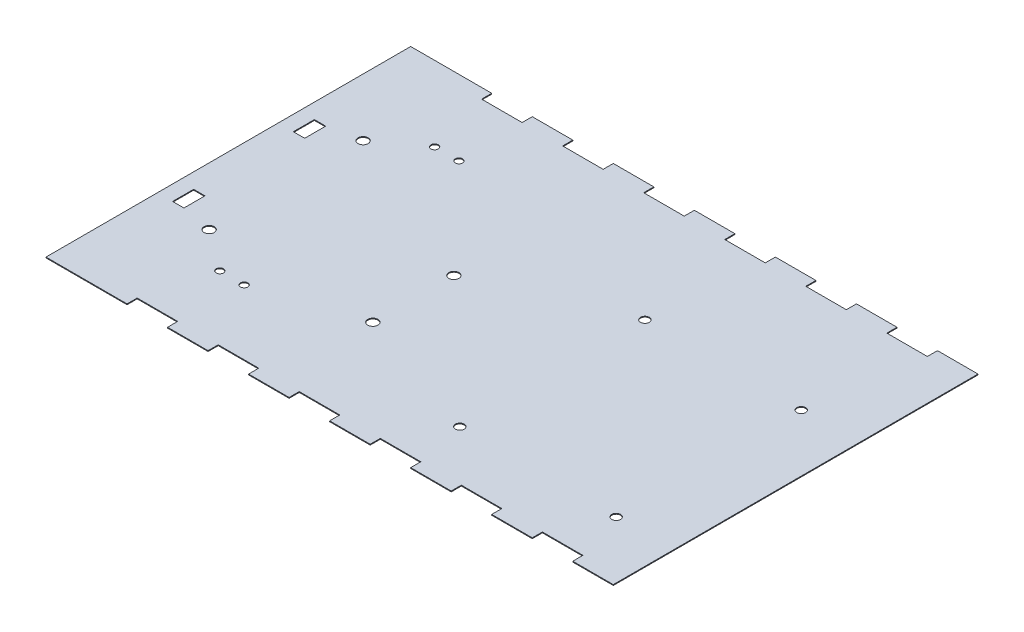
SolidWorks part; units mm, degrees
ref_plane "Front" through (0, 0, 0) normal (0, 0, 1) x (1, 0, 0)
ref_plane "Top" through (0, 0, 0) normal (0, 1, 0) x (1, 0, 0)
ref_plane "Right" through (0, 0, 0) normal (1, 0, 0) x (0, 0, -1)
sketch "Sketch1" plane through (0, 0, 0) normal (0, 1, 0) x (1, 0, 0)
  line L1 (-88.9, -57.15) -> (88.9, -57.15)
  line L2 (-88.9, -57.15) -> (-88.9, 57.15)
  line L3 (-88.9, 57.15) -> (88.9, 57.15)
  line L4 (88.9, -57.15) -> (88.9, 57.15)
  line L5 (-88.9, -57.15) -> (88.9, 57.15) construction
  line L6 (-88.9, 57.15) -> (88.9, -57.15) construction
  point P0 (0, 0)
  dimension "D1" = 177.8
  dimension "D2" = 114.3
extrude "Boss-Extrude1" add sketch "Sketch1" along normal blind 0.254
sketch "Sketch2" plane through (0, 0.254, 0) normal (0, 1, 0) x (1, 0, 0)
  line L0 (-73.152, -57.15) -> (-73.152, 57.15) construction
  line L1 (-88.9, -57.15) -> (88.9, -57.15) construction
  line L2 (88.9, 57.15) -> (-88.9, 57.15) construction
  line L3 (88.9, -57.15) -> (88.9, 57.15) construction
  line L4 (76.2, -57.15) -> (63.5, -57.15)
  line L5 (76.2, -57.15) -> (76.2, -53.975)
  line L6 (76.2, -53.975) -> (63.5, -53.975)
  line L7 (63.5, -57.15) -> (63.5, -53.975)
  line L8 (50.8, -57.15) -> (50.8, -53.975)
  line L9 (50.8, -57.15) -> (38.1, -57.15)
  line L10 (38.1, -57.15) -> (38.1, -53.975)
  line L11 (50.8, -53.975) -> (38.1, -53.975)
  line L12 (25.4, -57.15) -> (25.4, -53.975)
  line L13 (25.4, -57.15) -> (12.7, -57.15)
  line L14 (12.7, -57.15) -> (12.7, -53.975)
  line L15 (25.4, -53.975) -> (12.7, -53.975)
  line L16 (0, -57.15) -> (0, -53.975)
  line L17 (0, -57.15) -> (-12.7, -57.15)
  line L18 (-12.7, -57.15) -> (-12.7, -53.975)
  line L19 (0, -53.975) -> (-12.7, -53.975)
  line L20 (-25.4, -57.15) -> (-25.4, -53.975)
  line L21 (-25.4, -57.15) -> (-38.1, -57.15)
  line L22 (-38.1, -57.15) -> (-38.1, -53.975)
  line L23 (-25.4, -53.975) -> (-38.1, -53.975)
  line L24 (-50.8, -57.15) -> (-50.8, -53.975)
  line L25 (-50.8, -57.15) -> (-63.5, -57.15)
  line L26 (-63.5, -57.15) -> (-63.5, -53.975)
  line L27 (-50.8, -53.975) -> (-63.5, -53.975)
  line L28 (-88.9, 0) -> (88.9, 0) construction
  line L29 (-88.9, 57.15) -> (-88.9, -57.15) construction
  line L30 (76.2, 53.975) -> (63.5, 53.975)
  line L31 (63.5, 57.15) -> (63.5, 53.975)
  line L32 (76.2, 57.15) -> (63.5, 57.15)
  line L33 (76.2, 57.15) -> (76.2, 53.975)
  line L34 (50.8, 57.15) -> (38.1, 57.15)
  line L35 (38.1, 57.15) -> (38.1, 53.975)
  line L36 (50.8, 53.975) -> (38.1, 53.975)
  line L37 (50.8, 57.15) -> (50.8, 53.975)
  line L38 (25.4, 57.15) -> (12.7, 57.15)
  line L39 (12.7, 57.15) -> (12.7, 53.975)
  line L40 (25.4, 53.975) -> (12.7, 53.975)
  line L41 (25.4, 57.15) -> (25.4, 53.975)
  line L42 (0, 57.15) -> (-12.7, 57.15)
  line L43 (-12.7, 57.15) -> (-12.7, 53.975)
  line L44 (0, 53.975) -> (-12.7, 53.975)
  line L45 (0, 57.15) -> (0, 53.975)
  line L46 (-25.4, 57.15) -> (-38.1, 57.15)
  line L47 (-38.1, 57.15) -> (-38.1, 53.975)
  line L48 (-25.4, 53.975) -> (-38.1, 53.975)
  line L49 (-25.4, 57.15) -> (-25.4, 53.975)
  line L50 (-50.8, 57.15) -> (-63.5, 57.15)
  line L51 (-63.5, 57.15) -> (-63.5, 53.975)
  line L52 (-50.8, 53.975) -> (-63.5, 53.975)
  line L53 (-50.8, 57.15) -> (-50.8, 53.975)
  circle A0 centre (-57.912, -33.655) radius 1.143
  circle A1 centre (-50.292, -33.655) radius 1.143
  circle A2 centre (-50.292, 33.655) radius 1.143
  circle A3 centre (-57.912, 33.655) radius 1.143
  dimension "D8" = 2.286
  dimension "D9" = 23.495
  dimension "D1" = 162.052
  dimension "D2" = 3.175
  dimension "D3" = 12.7
  dimension "D4" = 12.7
  dimension "D6" = 15.24
  dimension "D7" = 7.62
  dimension "D5" = 6
extrude "Cut-Extrude1" cut sketch "Sketch2" against normal through all
sketch "Sketch3" plane through (0, 0.254, 0) normal (0, 1, 0) x (1, 0, 0)
  line L0 (-88.9, 0) -> (88.9, 0) construction
  line L1 (18.5965, 43.2622) -> (74.4765, 43.2622) construction
  line L2 (18.5965, 43.2622) -> (18.5965, -41.8278) construction
  line L3 (18.5965, -41.8278) -> (74.4765, -41.8278) construction
  line L4 (74.4765, 43.2622) -> (74.4765, -41.8278) construction
  line L5 (-74.8, 26.65) -> (0, 26.65) construction
  line L6 (-74.8, 26.65) -> (-74.8, -26.65) construction
  line L7 (-74.8, -26.65) -> (0, -26.65) construction
  line L8 (0, 26.65) -> (0, -26.65) construction
  line L9 (-88.9, 57.15) -> (-88.9, -57.15) construction
  line L10 (-84.1583, 22.225) -> (-80.6023, 22.225)
  line L11 (-84.1583, 22.225) -> (-84.1583, 15.621)
  line L12 (-84.1583, 15.621) -> (-80.6023, 15.621)
  line L13 (-80.6023, 22.225) -> (-80.6023, 15.621)
  line L14 (-84.1583, -15.621) -> (-80.6023, -15.621)
  line L15 (-84.1583, -15.621) -> (-84.1583, -22.225)
  line L16 (-84.1583, -22.225) -> (-80.6023, -22.225)
  line L17 (-80.6023, -15.621) -> (-80.6023, -22.225)
  line L18 (88.9, -57.15) -> (88.9, 57.15) construction
  line L19 (-88.9, -23.622) -> (88.9, -23.622) construction
  circle A0 centre (70.9765, -38.3278) radius 1.375
  circle A1 centre (21.9765, -38.3278) radius 1.375
  circle A2 centre (21.9765, 19.6722) radius 1.375
  circle A3 centre (70.9765, 19.6722) radius 1.375
  circle A4 centre (-70.7865, -24.13) radius 1.5875
  circle A6 centre (-70.7865, 24.13) radius 1.5875
  circle A7 centre (-19.9891, -23.622) radius 1.5875
  circle A8 centre (-19.9891, 1.778) radius 1.5875
  dimension "D7" = 2.75
  dimension "D18" = 3.175
  dimension "D1" = 55.88
  dimension "D2" = 85.09
  dimension "D3" = 53.3
  dimension "D4" = 74.8
  dimension "D5" = 3.5
  dimension "D6" = 49
  dimension "D8" = 58
  dimension "D9" = 3.5
  dimension "D10" = 44.45
  dimension "D11" = 6.604
  dimension "D12" = 3.556
  dimension "D13" = 6.604
  dimension "D14" = 3.556
  dimension "D15" = 22.225
  dimension "D16" = 4.7417
  dimension "D17" = 23.622
  dimension "D19" = 0.508
  dimension "D20" = 4.0135
  dimension "D21" = 50.8
  dimension "D22" = 2
extrude "Cut-Extrude2" cut sketch "Sketch3" against normal through all
